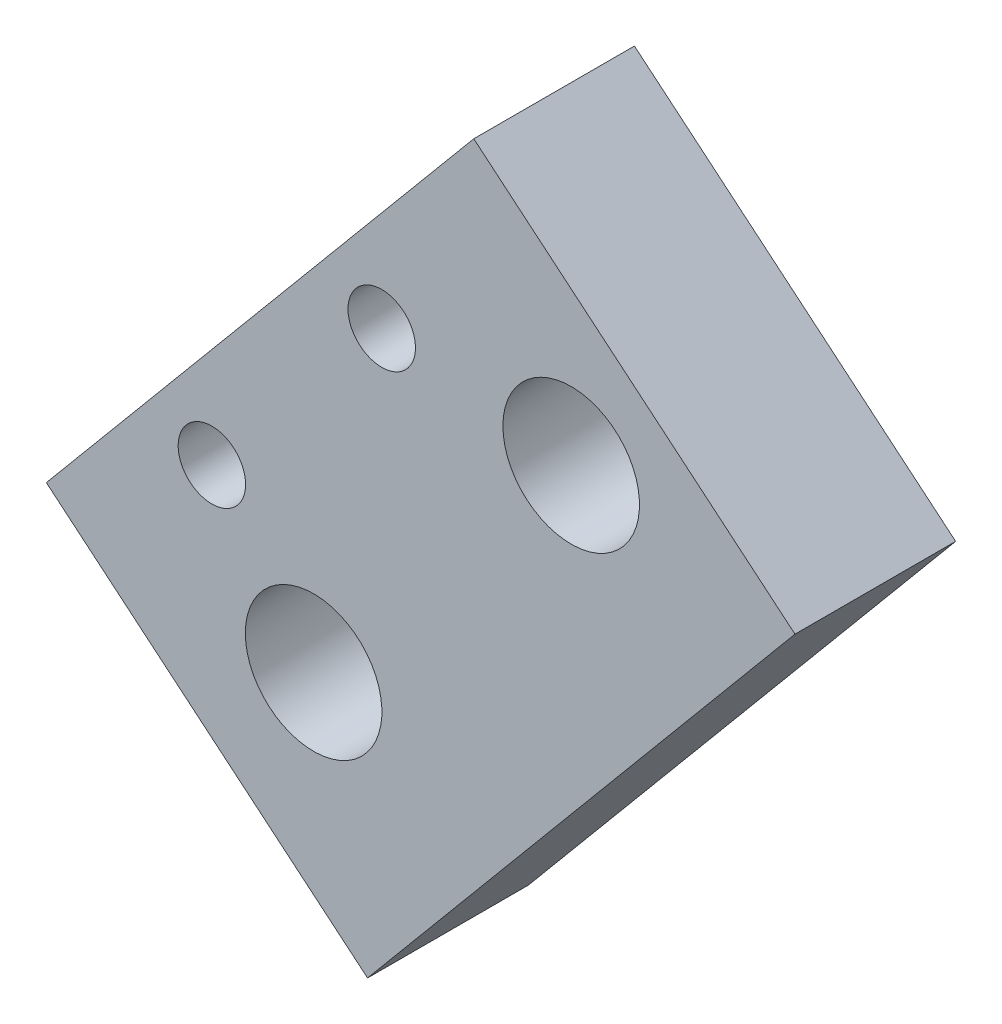
SolidWorks part; units mm, degrees
ref_plane "Front Plane" through (0, 0, 0) normal (0, 0, 1) x (1, 0, 0)
ref_plane "Top Plane" through (0, 0, 0) normal (0, 1, 0) x (1, 0, 0)
ref_plane "Right Plane" through (0, 0, 0) normal (1, 0, 0) x (0, 0, -1)
sketch "Sketch2" plane through (0, 0, 3306.8702) normal (0, 0, -1) x (-1, 0, 0)
  line L0 (-107.2871, 528.6308) -> (-87.2957, 545.3368)
  line L1 (-107.2871, 528.6308) -> (-80.6838, 496.7956)
  line L2 (-87.2957, 545.3368) -> (-60.6923, 513.5017)
  line L3 (-80.6838, 496.7956) -> (-60.6923, 513.5017)
  circle A0 centre (-77.327, 511.5826) radius 4.25
  circle A1 centre (-93.3579, 530.7661) radius 4.25
  circle A3 centre (-81.5669, 532.2512) radius 2.1
  circle A4 centre (-70.9945, 519.5996) radius 2.1
  circle A8 centre (81.151, 512.2482) radius 11 construction
  dimension "D3" = 8.5
  dimension "D4" = 8.5
  dimension "D5" = 3.9951
  dimension "D1" = 7.2934
  dimension "D2" = 11.2854
  dimension "D6" = 13.7146
  dimension "D7" = 9.1942
  dimension "D8" = 3.9951
  dimension "D9" = 12.0578
  dimension "D10" = 12.0578
extrude "Boss-Extrude1" add sketch "Sketch2" along normal blind 10
